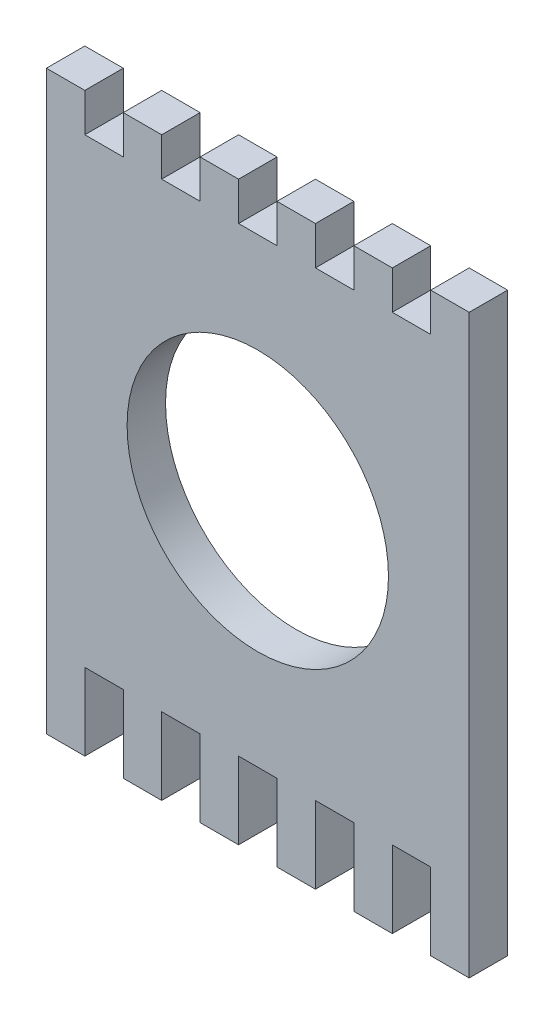
SolidWorks part; units mm, degrees
ref_plane "Plan de face" through (0, 0, 0) normal (0, 0, 1) x (1, 0, 0)
ref_plane "Plan de dessus" through (0, 0, 0) normal (0, 1, 0) x (1, 0, 0)
ref_plane "Plan de droite" through (0, 0, 0) normal (1, 0, 0) x (0, 0, -1)
sketch "Esquisse1" plane through (0, 0, 0) normal (0, 0, 1) x (1, 0, 0)
  line L0 (10, 65) -> (15, 65)
  line L1 (0, 0) -> (55, 0)
  line L2 (0, 0) -> (0, 60)
  line L3 (0, 60) -> (55, 60)
  line L4 (55, 0) -> (55, 60)
  line L5 (0, 60) -> (5, 60)
  line L6 (0, 60) -> (0, 65)
  line L7 (0, 65) -> (5, 65)
  line L8 (5, 60) -> (5, 65)
  line L9 (15, 60) -> (15, 65)
  line L10 (10, 60) -> (10, 65)
  line L11 (20, 65) -> (25, 65)
  line L12 (25, 60) -> (25, 65)
  line L13 (20, 60) -> (20, 65)
  line L14 (30, 65) -> (35, 65)
  line L15 (35, 60) -> (35, 65)
  line L16 (30, 60) -> (30, 65)
  line L17 (40, 65) -> (45, 65)
  line L18 (45, 60) -> (45, 65)
  line L19 (40, 60) -> (40, 65)
  line L20 (50, 65) -> (55, 65)
  line L21 (55, 60) -> (55, 65)
  line L22 (50, 60) -> (50, 65)
  line L23 (15, 0) -> (15, -10)
  line L24 (0, 0) -> (5, 0)
  line L25 (0, 0) -> (0, -10)
  line L26 (0, -10) -> (5, -10)
  line L27 (5, 0) -> (5, -10)
  line L28 (10, 0) -> (10, -10)
  line L29 (10, -10) -> (15, -10)
  line L30 (25, 0) -> (25, -10)
  line L31 (20, 0) -> (20, -10)
  line L32 (20, -10) -> (25, -10)
  line L33 (35, 0) -> (35, -10)
  line L34 (30, 0) -> (30, -10)
  line L35 (30, -10) -> (35, -10)
  line L36 (45, 0) -> (45, -10)
  line L37 (40, 0) -> (40, -10)
  line L38 (40, -10) -> (45, -10)
  line L39 (55, 0) -> (55, -10)
  line L40 (50, 0) -> (50, -10)
  line L41 (50, -10) -> (55, -10)
  circle A0 centre (27.5, 30) radius 17
  dimension "D3" = 34
  dimension "D1" = 60
  dimension "D2" = 55
  dimension "D4" = 27.5
  dimension "D5" = 30
  dimension "D6" = 5
  dimension "D7" = 5
  dimension "D9" = 5
  dimension "D10" = 10
  dimension "D8" = 6
  dimension "D11" = 6
extrude "Boss.-Extru.1" add sketch "Esquisse1" along normal blind 5 contours L1 L4 L3 L2 A0 | L10 L3 L9 L0 | L3 L8 L7 L6 | L13 L3 L12 L11 | L16 L3 L15 L14 | L22 L3 L21 L20 | L19 L3 L18 L17 | L27 L1 L25 L26 | L28 L29 L23 L1 | L31 L32 L30 L1 | L34 L35 L33 L1 | L37 L38 L36 L1 | L40 L41 L39 L1
